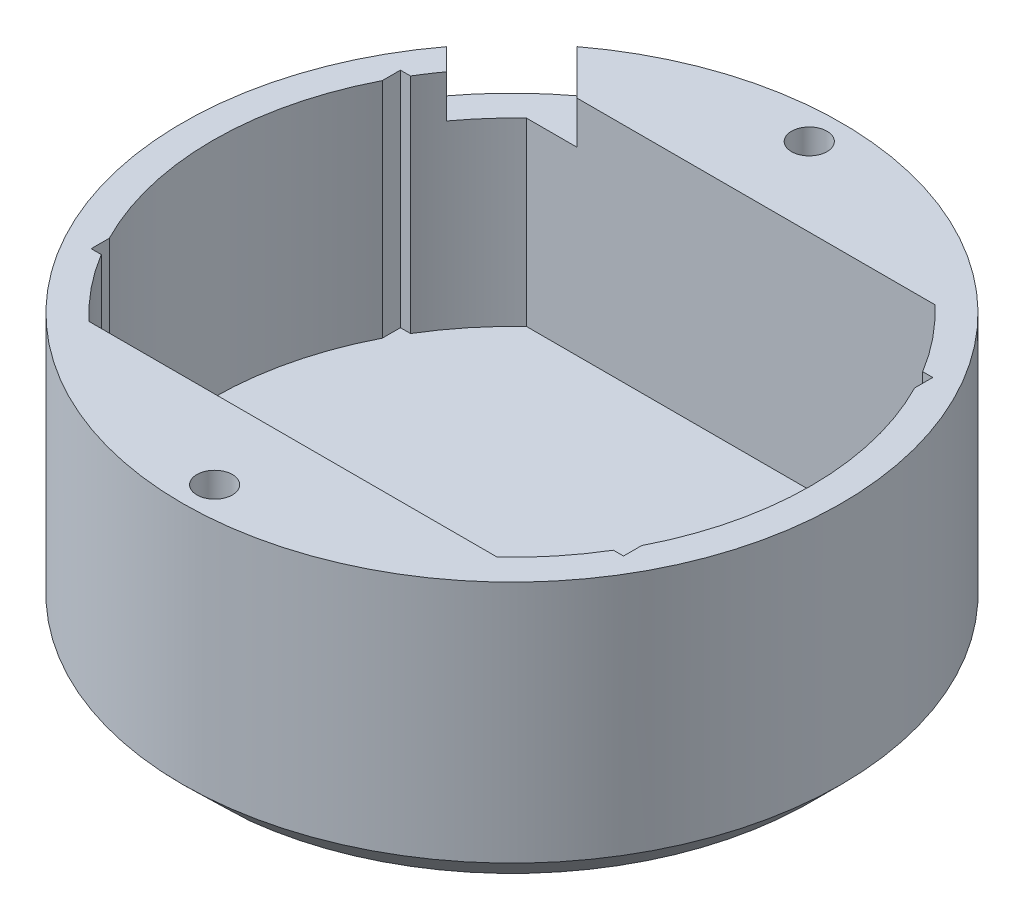
SolidWorks part; units mm, degrees
ref_plane "Front Plane" through (0, 0, 0) normal (0, 0, 1) x (1, 0, 0)
ref_plane "Top Plane" through (0, 0, 0) normal (0, 1, 0) x (1, 0, 0)
ref_plane "Right Plane" through (0, 0, 0) normal (1, 0, 0) x (0, 0, -1)
sketch "Sketch2" plane through (0, 0, 0) normal (0, 1, 0) x (1, 0, 0)
  circle A0 centre (0, 0) radius 32.5
  dimension "D1" = 65
extrude "Boss-Extrude1" add sketch "Sketch2" against normal blind 27
sketch "Sketch3" plane through (0, 0, 0) normal (0, 1, 0) x (1, 0, 0)
  circle A0 centre (0, 0) radius 29.5
  circle A1 centre (0, 0) radius 32.5 construction
  dimension "D1" = 3
extrude "Cut-Extrude1" cut sketch "Sketch3" against normal blind 22
chamfer "Chamfer1" distance 3 angle 45 1 edges at (0, -27, 32.5)
sketch "Sketch5" plane through (0, 0, 0) normal (0, 1, 0) x (1, 0, 0)
  line L0 (0, 32.5) -> (0, -32.5) construction
  line L1 (20.1242, -21.57) -> (-20.1242, -21.57)
  circle A0 centre (0, 0) radius 32.5 construction
  circle A2 centre (0, 0) radius 29.5 construction
  arc A3 (-20.1242, -21.57) -> (20.1242, -21.57) centre (0, 0) ccw
  point P7 (0, -21.57)
  point P8 (0, -27.57)
  dimension "D1" = 6
  dimension "D2" = 4.93
extrude "Boss-Extrude2" add sketch "Sketch5" against normal up to surface (22 mm away) up to face at (0, -22, 29.5)
sketch "Sketch6" plane through (0, -22, 0) normal (0, 1, 0) x (1, 0, 0)
  line L0 (29.5, 0) -> (-29.5, 0) construction
  line L2 (0, 29.5) -> (0, -21.57) construction
  line L3 (20.1242, -21.57) -> (-20.1242, -21.57) construction
  line L4 (26.25, 15.25) -> (-26.25, 15.25)
  line L5 (26.25, 15.25) -> (26.25, -15.25)
  line L6 (26.25, -15.25) -> (-26.25, -15.25)
  line L7 (-26.25, 15.25) -> (-26.25, -15.25)
  arc A0 (20.1242, -21.57) -> (-20.1242, -21.57) centre (0, 0) ccw construction
  arc A1 (20.1242, -21.57) -> (-20.1242, -21.57) centre (0, 0) ccw construction
  point P17 (0, 0)
  dimension "D1" = 30.5
  dimension "D2" = 52.5
extrude "Cut-Extrude3" cut sketch "Sketch6" along normal through all
mirror "Mirror1" about plane through (0, 0, 0) normal (0, 0, 1) of "Boss-Extrude2"
sketch "Sketch7" plane through (26.25, 0, 0) normal (-1, 0, 0) x (0, 0, 1)
  line L0 (15.25, -22) -> (13.4606, -22) construction
  point P0 (3.7206, 0)
  point P1 (3.7206, -22)
  dimension "D1" = 22
sketch "Sketch9" plane through (0, 0, 0) normal (0, 1, 0) x (1, 0, 0)
  line L0 (18.3612, -30.054) -> (10.709, -21.0717)
  line L1 (10.709, -21.0717) -> (20.4352, -12.7857)
  line L2 (20.4352, -12.7857) -> (28.3558, -22.083)
sketch "Sketch10" plane through (0, -27, 0) normal (0, -1, 0) x (1, 0, 0)
  line L0 (0, 32.5) -> (0, -32.5) construction
  line L1 (-32.5, 0) -> (32.5, 0) construction
  line L2 (-1.7321, -32.32) -> (1.7321, -32.32)
  line L3 (1.7321, -32.32) -> (3.4641, -29.32)
  line L4 (3.4641, -29.32) -> (1.7321, -26.32)
  line L5 (1.7321, -26.32) -> (-1.7321, -26.32)
  line L6 (-1.7321, -26.32) -> (-3.4641, -29.32)
  line L7 (-3.4641, -29.32) -> (-1.7321, -32.32)
  line L8 (-3.4641, 29.32) -> (-1.7321, 32.32)
  line L9 (-1.7321, 26.32) -> (-3.4641, 29.32)
  line L10 (1.7321, 26.32) -> (-1.7321, 26.32)
  line L11 (3.4641, 29.32) -> (1.7321, 26.32)
  line L12 (1.7321, 32.32) -> (3.4641, 29.32)
  line L13 (-1.7321, 32.32) -> (1.7321, 32.32)
  circle A0 centre (0, 0) radius 32.5 construction
  circle A1 centre (0, -29.32) radius 3 construction
  point P11 (-2.5981, -27.82)
  dimension "D1" = 6
  dimension "D2" = 3.18
extrude "Cut-Extrude4" cut sketch "Sketch10" against normal blind 6
ref_plane "Plane1" through (-22.981, 0, -22.981) normal (-0.7071, 0, -0.7071) x (0, 1, 0)
sketch "Sketch12" plane through (-22.981, 0, -22.981) normal (-0.7071, 0, -0.7071) x (0, 1, 0)
  line L0 (0, -32.5) -> (0, 32.5) construction
  line L5 (0, 4.55) -> (-4.2, 4.55)
  line L6 (0, 4.55) -> (0, -4.55)
  line L7 (0, -4.55) -> (-4.2, -4.55)
  line L8 (-4.2, 4.55) -> (-4.2, -4.55)
  point P6 (0, 0)
  dimension "D1" = 9.1
  dimension "D2" = 4.2
extrude "Cut-Extrude5" cut sketch "Sketch12" against normal blind 10
sketch "Sketch4" plane through (0, 0, 0) normal (0, 1, 0) x (1, 0, 0)
  line L0 (0, 32.5) -> (0, -32.5) construction
  line L1 (0, 0) -> (-32.5, 0) construction
  circle A1 centre (0, 29.32) radius 1.75
  circle A2 centre (0, -29.32) radius 1.75
  circle A4 centre (0, 0) radius 32.5 construction
  dimension "D1" = 3.5
  dimension "D2" = 90
  dimension "D3" = 3.18
  dimension "D4" = 3.18
extrude "Cut-Extrude2" cut sketch "Sketch4" against normal through all
